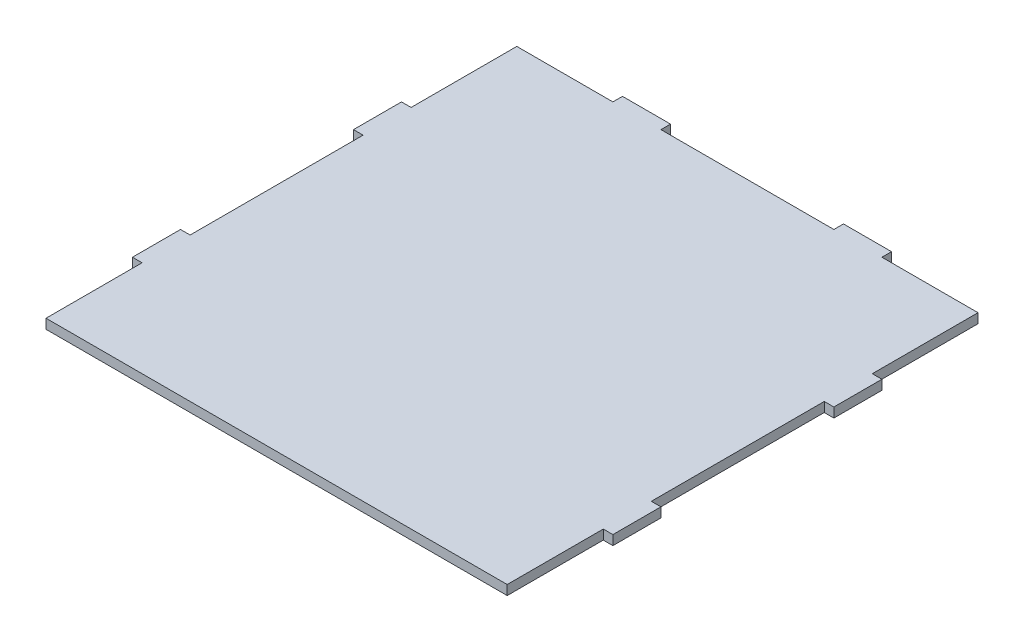
SolidWorks part; units mm, degrees
ref_plane "Front Plane" through (0, 0, 0) normal (0, 0, 1) x (1, 0, 0)
ref_plane "Top Plane" through (0, 0, 0) normal (0, 1, 0) x (1, 0, 0)
ref_plane "Right Plane" through (0, 0, 0) normal (1, 0, 0) x (0, 0, -1)
sketch "Sketch1" plane through (0, 0, 0) normal (0, 0, 1) x (1, 0, 0)
  line L0 (48, 50) -> (48, -50) construction
  line L1 (-48, -50) -> (48, -50)
  line L2 (-48, -50) -> (-48, -48)
  line L3 (-48, -48) -> (48, -48)
  line L4 (48, -50) -> (48, -48)
  dimension "D1" = 2
extrude "Boss-Extrude1" add sketch "Sketch1" along normal up to surface (98 mm away)
sketch "Sketch2" plane through (-48, 0, 0) normal (-1, 0, 0) x (0, 0, 1)
  line L0 (98, -48) -> (0, -48) construction
  line L1 (78, -48) -> (68, -48)
  line L2 (78, -48) -> (78, -50)
  line L3 (78, -50) -> (68, -50)
  line L4 (68, -48) -> (68, -50)
  line L5 (98, -50) -> (0, -50) construction
  line L6 (98, -50) -> (98, -48) construction
  point P10 (98, -49)
  dimension "D1" = 20
  dimension "D2" = 30
extrude "Boss-Extrude2" add sketch "Sketch2" along normal up to surface (2 mm away)
ref_plane "Plane1" through (0, 0, 50) normal (0, 0, 1) x (1, 0, 0)
mirror "Mirror1" about plane through (0, 0, 50) normal (0, 0, 1) of "Boss-Extrude2"
sketch "Sketch3" plane through (48, 0, 0) normal (1, 0, 0) x (0, 0, -1)
  line L0 (-98, -50) -> (0, -50) construction
  line L1 (-78, -50) -> (-68, -50)
  line L2 (-78, -50) -> (-78, -48)
  line L3 (-78, -48) -> (-68, -48)
  line L4 (-68, -50) -> (-68, -48)
  line L5 (-98, -48) -> (0, -48) construction
  line L6 (-98, -48) -> (-98, -50) construction
  point P10 (-98, -49)
  dimension "D1" = 30
  dimension "D2" = 20
extrude "Boss-Extrude3" add sketch "Sketch3" along normal up to surface (2 mm away)
mirror "Mirror2" about plane through (0, 0, 50) normal (0, 0, 1) of "Boss-Extrude3"
sketch "Sketch4" plane through (0, 0, 0) normal (0, 0, -1) x (-1, 0, 0)
  line L0 (-48, -48) -> (48, -48) construction
  line L1 (28, -48) -> (18, -48)
  line L2 (28, -48) -> (28, -50)
  line L3 (28, -50) -> (18, -50)
  line L4 (18, -48) -> (18, -50)
  line L5 (48, -50) -> (-48, -50) construction
  line L6 (48, -48) -> (48, -50) construction
  point P10 (48, -49)
  dimension "D1" = 20
  dimension "D2" = 30
extrude "Boss-Extrude4" add sketch "Sketch4" along normal up to surface (2 mm away)
mirror "Mirror3" about plane through (0, 0, 0) normal (1, 0, 0) of "Boss-Extrude4"
